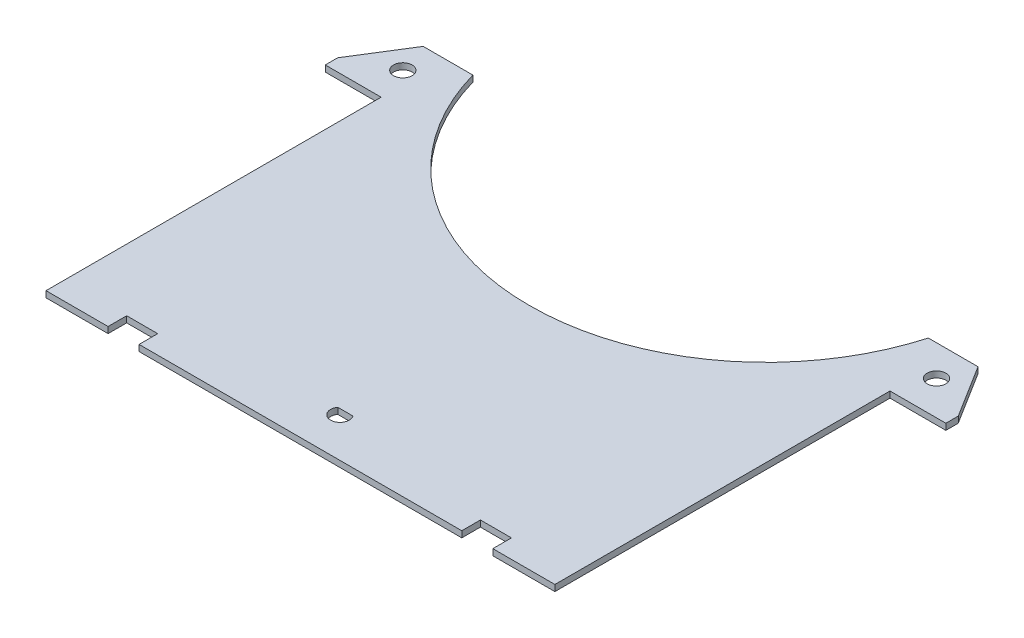
SolidWorks part; units mm, degrees
ref_plane "Plano frontal" through (0, 0, 0) normal (0, 0, 1) x (1, 0, 0)
ref_plane "Plano superior" through (0, 0, 0) normal (0, 1, 0) x (1, 0, 0)
ref_plane "Plano direito" through (0, 0, 0) normal (1, 0, 0) x (0, 0, -1)
sketch "Base" plane through (0, 0, 0) normal (0, 1, 0) x (1, 0, 0)
  line L0 (0, 56.1403) -> (5.2992, 64.6208)
  line L9 (0, 56.1403) -> (0, 54.1403)
  line L10 (0, 54.1403) -> (9, 54.1403)
  line L11 (9, 54.1403) -> (9, 0.1403)
  line L12 (9, 0.1403) -> (19, 0.1403)
  line L13 (19, 0.1403) -> (19, 3.1403)
  line L14 (19, 3.1403) -> (24, 3.1403)
  line L15 (24, 3.1403) -> (24, 0.1403)
  line L16 (24, 0.1403) -> (76, 0.1403)
  line L17 (5.2992, 64.6208) -> (13.2992, 64.6208)
  line L20 (94.7008, 64.6208) -> (86.7008, 64.6208)
  line L21 (76, 3.1403) -> (76, 0.1403)
  line L22 (81, 3.1403) -> (76, 3.1403)
  line L23 (81, 0.1403) -> (81, 3.1403)
  line L24 (91, 0.1403) -> (81, 0.1403)
  line L25 (91, 54.1403) -> (91, 0.1403)
  line L26 (100, 54.1403) -> (91, 54.1403)
  line L27 (100, 56.1403) -> (100, 54.1403)
  line L28 (100, 56.1403) -> (94.7008, 64.6208)
  line L29 (48.7817, 7.375) -> (51.2183, 7.375)
  arc A0 (48.7817, 7.375) -> (51.2183, 7.375) centre (50, 6.5) ccw
  circle A1 centre (7, 59.6403) radius 1.5
  arc A3 (13.2992, 64.6208) -> (50, 37.0203) centre (49.8486, 75.02) ccw
  arc A4 (86.7008, 64.6208) -> (50, 37.0203) centre (50.1514, 75.02) cw
  circle A5 centre (93, 59.6403) radius 1.5
  dimension "D8" = 148
  dimension "D10" = 8
  dimension "D12" = 38
  dimension "D2" = 10
  dimension "D3" = 2
  dimension "D4" = 9
  dimension "D5" = 54
  dimension "D6" = 10
  dimension "D7" = 5
  dimension "D9" = 3
extrude "Ressalto-extrusão1" add sketch "Base" along normal blind 1
